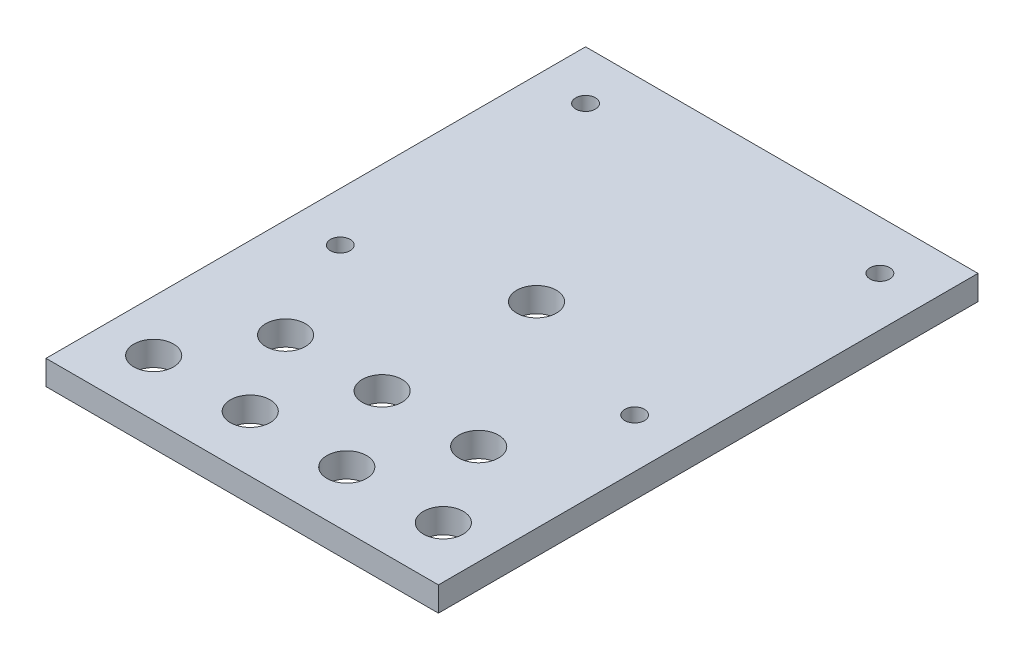
SolidWorks part; units mm, degrees
ref_plane "Front Plane" through (0, 0, 0) normal (0, 0, 1) x (1, 0, 0)
ref_plane "Top Plane" through (0, 0, 0) normal (0, 1, 0) x (1, 0, 0)
ref_plane "Right Plane" through (0, 0, 0) normal (1, 0, 0) x (0, 0, -1)
sketch "Sketch1" plane through (0, 0, 0) normal (0, 1, 0) x (1, 0, 0)
  line L1 (0, 0) -> (101.6, 0)
  line L2 (0, 0) -> (0, 139.7)
  line L3 (0, 139.7) -> (101.6, 139.7)
  line L4 (101.6, 0) -> (101.6, 139.7)
  dimension "D1" = 101.6
  dimension "D2" = 139.7
extrude "Boss-Extrude1" add sketch "Sketch1" along normal blind 6.35
sketch "Sketch2" plane through (0, 6.35, 0) normal (0, 1, 0) x (1, 0, 0)
  line L0 (88.3, 14.5747) -> (63.3, 14.5747) construction
  line L1 (38.3, 14.5747) -> (63.3, 14.5747) construction
  line L2 (0, 139.7) -> (0, 0) construction
  line L3 (50.8, 36.2253) -> (50.8, 14.5747) construction
  line L4 (0, 0) -> (101.6, 0) construction
  line L5 (101.6, 139.7) -> (0, 139.7) construction
  line L6 (101.6, 0) -> (101.6, 139.7) construction
  circle A0 centre (13.3, 14.5747) radius 5.1435
  circle A1 centre (38.3, 14.5747) radius 5.1435
  circle A2 centre (63.3, 14.5747) radius 5.1435
  circle A3 centre (88.3, 14.5747) radius 5.1435
  circle A4 centre (75.8, 36.2253) radius 5.1435
  circle A6 centre (50.8, 36.2253) radius 5.1435
  circle A7 centre (25.8, 36.2253) radius 5.1435
  circle A8 centre (12.7, 63.5) radius 2.55
  circle A9 centre (12.7, 127) radius 2.55
  circle A10 centre (88.9, 63.5) radius 2.55
  circle A11 centre (88.9, 127) radius 2.55
  circle A12 centre (50.8, 76.2) radius 5.1435
  point P2 (50.8, 14.5747)
  point P13 (75.8, 14.5747)
  point P14 (50.8, 25.4)
  point P36 (0, 0)
  dimension "D1" = 10.287
  dimension "D4" = 10.287
  dimension "D6" = 25.4
  dimension "D8" = 5.1
  dimension "D11" = 5.1
  dimension "D15" = 5.1
  dimension "D18" = 5.1
  dimension "D21" = 10.287
  dimension "D3" = 50.8
  dimension "D5" = 21.6506
  dimension "D9" = 63.5
  dimension "D10" = 12.7
  dimension "D12" = 12.7
  dimension "D13" = 12.7
  dimension "D14" = 25
  dimension "D16" = 12.7
  dimension "D17" = 63.5
  dimension "D19" = 12.7
  dimension "D20" = 12.7
  dimension "D22" = 12.7
  dimension "D2" = 4
  dimension "D7" = 3
extrude "Cut-Extrude1" cut sketch "Sketch2" against normal through all
